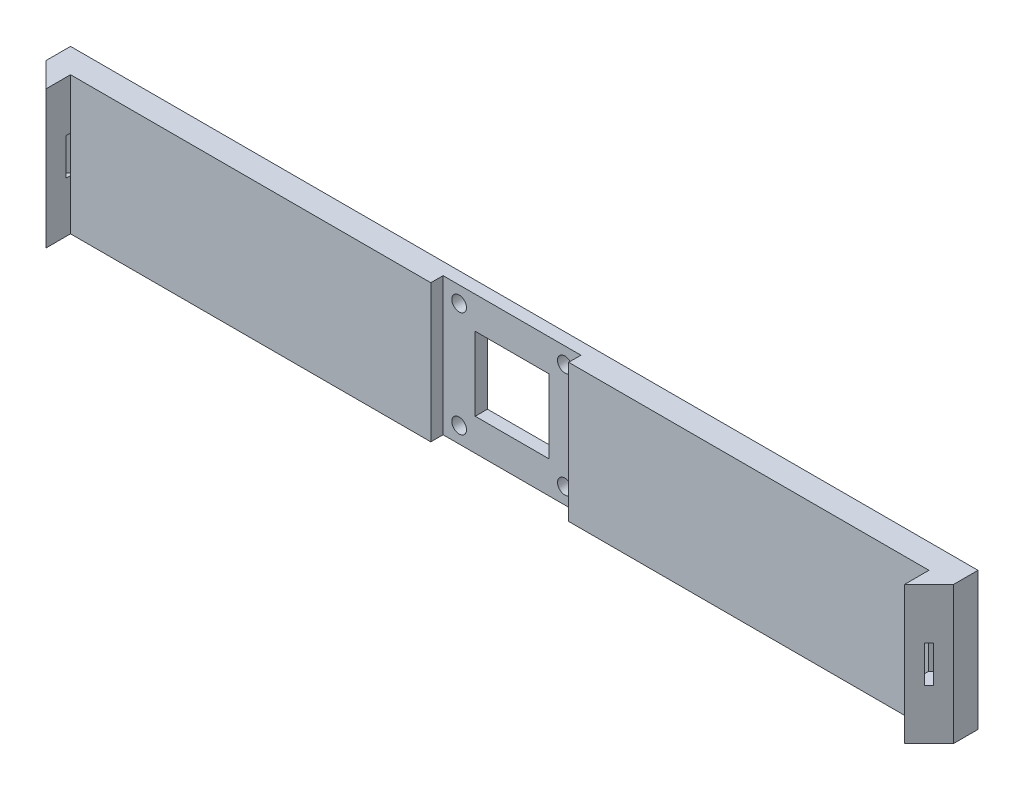
SolidWorks part; units mm, degrees
ref_plane "Front Plane" through (0, 0, 0) normal (0, 0, 1) x (1, 0, 0)
ref_plane "Top Plane" through (0, 0, 0) normal (0, 1, 0) x (1, 0, 0)
ref_plane "Right Plane" through (0, 0, 0) normal (1, 0, 0) x (0, 0, -1)
sketch "Sketch1" plane through (0, 0, 0) normal (0, 0, 1) x (1, 0, 0)
  line L1 (-175, -28.1) -> (175, -28.1)
  line L2 (-175, -28.1) -> (-175, 28.1)
  line L3 (-175, 28.1) -> (175, 28.1)
  line L4 (175, -28.1) -> (175, 28.1)
  line L5 (-175, -28.1) -> (175, 28.1) construction
  line L6 (-175, 28.1) -> (175, -28.1) construction
  point P0 (0, 0)
extrude "Boss-Extrude1" add sketch "Sketch1" along normal blind 10
sketch "Sketch2" plane through (0, 0, 10) normal (0, 0, 1) x (1, 0, 0)
  line L2 (175, 28.1) -> (-175, 28.1) construction
  line L3 (-28.1, -28.1) -> (28.1, -28.1)
  line L4 (-28.1, -28.1) -> (-28.1, 28.1)
  line L5 (-28.1, 28.1) -> (28.1, 28.1)
  line L6 (28.1, -28.1) -> (28.1, 28.1)
  point P8 (0, 0)
extrude "Cut-Extrude1" cut sketch "Sketch2" against normal blind 5
sketch "Sketch3" plane through (175, 0, 0) normal (1, 0, 0) x (0, 0, -1)
  line L1 (-10, 28.1) -> (0, 28.1)
  line L2 (-10, 28.1) -> (-10, -28.1)
  line L3 (-10, -28.1) -> (0, -28.1)
  line L4 (0, 28.1) -> (0, -28.1)
extrude "Boss-Extrude2" add sketch "Sketch3" along normal blind 10
sketch "Sketch4" plane through (0, 0, 10) normal (0, 0, 1) x (1, 0, 0)
  line L0 (28.1, -28.1) -> (185, -28.1) construction
  line L1 (185, 28.1) -> (175, 28.1)
  line L2 (185, 28.1) -> (185, -28.1)
  line L3 (185, -28.1) -> (175, -28.1)
  line L4 (175, 28.1) -> (175, -28.1)
extrude "Boss-Extrude3" add sketch "Sketch4" along normal blind 10
sketch "Sketch5" plane through (0, 28.1, 0) normal (0, 1, 0) x (1, 0, 0)
  line L0 (175, -20) -> (185, -10)
  line L1 (185, 0) -> (185, -20) construction
  line L2 (185, -10) -> (185, -20)
  line L3 (185, -20) -> (175, -20)
extrude "Cut-Extrude2" cut sketch "Sketch5" against normal blind 56.2
sketch "Sketch6" plane through (-175, 0, 0) normal (-1, 0, 0) x (0, 0, 1)
  line L1 (0, -28.1) -> (10, -28.1)
  line L2 (0, -28.1) -> (0, 28.1)
  line L3 (0, 28.1) -> (10, 28.1)
  line L4 (10, -28.1) -> (10, 28.1)
extrude "Boss-Extrude4" add sketch "Sketch6" along normal blind 10
sketch "Sketch7" plane through (0, 0, 10) normal (0, 0, 1) x (1, 0, 0)
  line L0 (-28.1, 28.1) -> (-185, 28.1) construction
  line L1 (-185, -28.1) -> (-175, -28.1)
  line L2 (-185, -28.1) -> (-185, 28.1)
  line L3 (-185, 28.1) -> (-175, 28.1)
  line L4 (-175, -28.1) -> (-175, 28.1)
extrude "Boss-Extrude5" add sketch "Sketch7" along normal blind 10
sketch "Sketch8" plane through (0, 28.1, 0) normal (0, 1, 0) x (1, 0, 0)
  line L0 (-175, -20) -> (-185, -10)
  line L1 (-185, -20) -> (-185, 0) construction
  line L2 (-185, -10) -> (-185, -20)
  line L3 (-185, -20) -> (-175, -20)
extrude "Cut-Extrude3" cut sketch "Sketch8" against normal blind 56.2
sketch "Sketch9" plane through (0, 0, 5) normal (0, 0, 1) x (1, 0, 0)
  line L3 (-15, -15) -> (15, -15)
  line L4 (-15, -15) -> (-15, 15)
  line L5 (-15, 15) -> (15, 15)
  line L6 (15, -15) -> (15, 15)
  point P4 (0, 0)
extrude "Cut-Extrude4" cut sketch "Sketch9" against normal blind 5
sketch "Sketch10" plane through (0, 0, 5) normal (0, 0, 1) x (1, 0, 0)
  circle A2 centre (21.55, 21.55) radius 3
  circle A3 centre (-21.55, -21.55) radius 3
  circle A4 centre (-21.55, 21.55) radius 3
  circle A5 centre (21.55, -21.55) radius 3
extrude "Cut-Extrude5" cut sketch "Sketch10" against normal blind 5
sketch "Sketch11" plane through (97.5, 0, 97.5) normal (0.7071, 0, 0.7071) x (0.7071, 0, -0.7071)
  line L3 (117.9226, -7.5) -> (115.4226, -7.5)
  line L4 (117.9226, -7.5) -> (117.9226, 7.5)
  line L5 (117.9226, 7.5) -> (115.4226, 7.5)
  line L6 (115.4226, -7.5) -> (115.4226, 7.5)
  line L7 (117.9226, -7.5) -> (115.4226, 7.5) construction
  line L8 (117.9226, 7.5) -> (115.4226, -7.5) construction
  point P6 (116.6726, 0)
extrude "Cut-Extrude6" cut sketch "Sketch11" against normal blind 7
sketch "Sketch12" plane through (-97.5, 0, 97.5) normal (-0.7071, 0, 0.7071) x (0.7071, 0, 0.7071)
  line L2 (-117.9226, 7.5) -> (-115.4226, 7.5)
  line L3 (-117.9226, 7.5) -> (-117.9226, -7.5)
  line L4 (-117.9226, -7.5) -> (-115.4226, -7.5)
  line L5 (-115.4226, 7.5) -> (-115.4226, -7.5)
  line L6 (-117.9226, 7.5) -> (-115.4226, -7.5) construction
  line L7 (-117.9226, -7.5) -> (-115.4226, 7.5) construction
  point P4 (-116.6726, 0)
extrude "Cut-Extrude7" cut sketch "Sketch12" against normal blind 7
